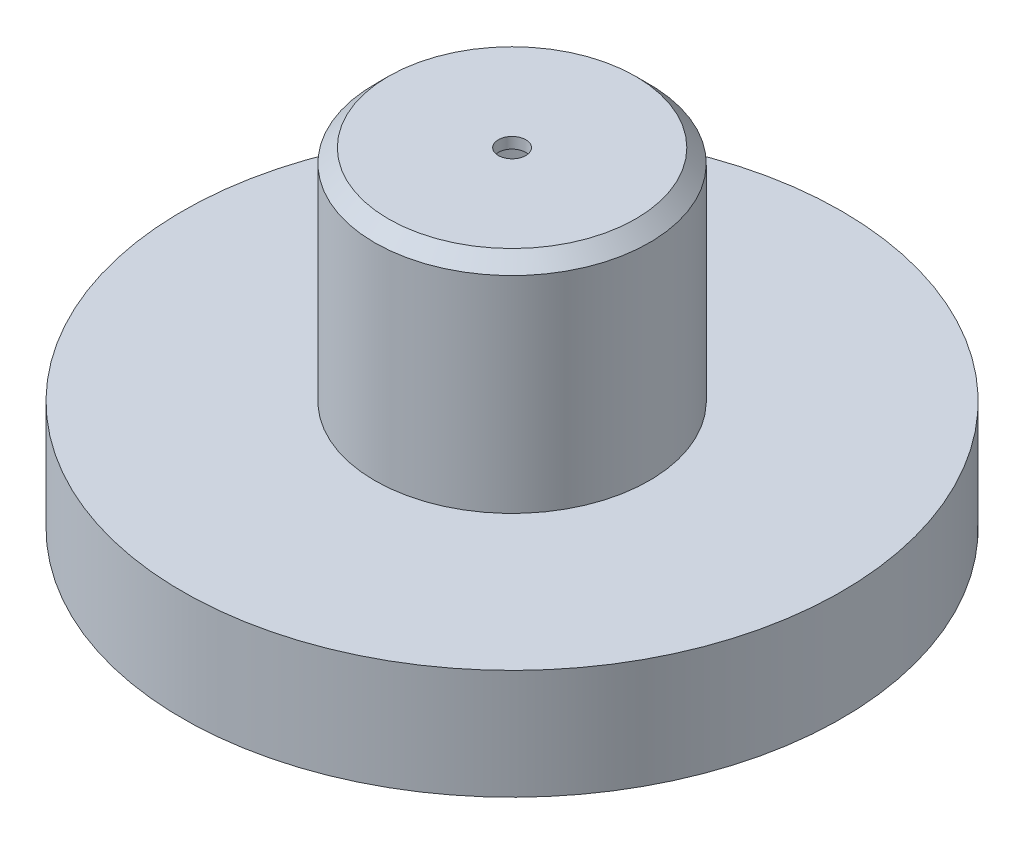
SolidWorks part; units mm, degrees
material "Alloy Steel"
ref_plane "Front Plane" through (0, 0, 0) normal (0, 0, 1) x (1, 0, 0)
ref_plane "Top Plane" through (0, 0, 0) normal (0, 1, 0) x (1, 0, 0)
ref_plane "Right Plane" through (0, 0, 0) normal (1, 0, 0) x (0, 0, -1)
sketch "Sketch2" plane through (0, 0, 0) normal (0, 0, 1) x (1, 0, 0)
  line L0 (55, 0) -> (-55, 0) construction
  line L1 (-75, 50) -> (-70, 50)
  line L2 (-75, 50) -> (-75, 15)
  line L3 (-75, -50) -> (-70, -50)
  line L4 (75, 50) -> (75, 15)
  line L5 (-75, 50) -> (75, -50) construction
  line L6 (-75, -50) -> (75, 50) construction
  line L7 (0, 50) -> (0, -74.3862) construction
  line L8 (-75, -15) -> (-75, -50)
  line L9 (75, -15) -> (75, -50)
  line L10 (-82.5762, 0) -> (133.8676, 0) construction
  line L11 (-60, 50) -> (-35, 50)
  line L12 (-25, 50) -> (25, 50)
  line L13 (35, 50) -> (60, 50)
  line L14 (70, 50) -> (75, 50)
  line L15 (-60, -50) -> (-35, -50)
  line L16 (-25, -50) -> (25, -50)
  line L17 (35, -50) -> (60, -50)
  line L18 (70, -50) -> (75, -50)
  line L19 (-35, 50) -> (-25, 50)
  line L20 (25, 50) -> (35, 50)
  arc A0 (-75, 15) -> (-75, -15) centre (-100.9808, 0) cw
  arc A1 (75, 15) -> (75, -15) centre (100.9808, 0) ccw
  arc A3 (-70, 50) -> (-60, 50) centre (-65, 50) ccw
  arc A4 (-35, -50) -> (-25, -50) centre (-30, -50) cw
  arc A5 (-70, -50) -> (-60, -50) centre (-65, -50) cw
  arc A6 (70, 50) -> (60, 50) centre (65, 50) cw
  arc A8 (70, -50) -> (60, -50) centre (65, -50) ccw
  arc A9 (35, -50) -> (25, -50) centre (30, -50) ccw
  point P0 (0, 0)
  dimension "D3" = 30
  dimension "D8" = 10
  dimension "D1" = 100
  dimension "D2" = 150
  dimension "D4" = 15
  dimension "D5" = 15
  dimension "D7" = 10
extrude "Boss-Extrude1" add sketch "Sketch2" along normal mid plane 200
sketch "Sketch3" plane through (0, 50, 0) normal (0, 1, 0) x (1, 0, 0)
  circle A0 centre (0, 0) radius 55
  circle A1 centre (0, 0) radius 50
  dimension "D1" = 110
  dimension "D2" = 100
extrude "Boss-Extrude3" add sketch "Sketch3" along normal blind 80 contours A1
chamfer "Chamfer1" distance 5 angle 45 1 edges at (0, 130, 50)
fillet "Fillet1" radius 1 4 edges at (75, -50, 0) (-75, -50, 0) (-75, 50, 0) (75, 50, 0)
sketch "Sketch4" plane through (0, -50, 0) normal (0, -1, 0) x (1, 0, 0)
  line L0 (132, 0) -> (-132, 0) construction
  line L1 (0, -132) -> (0, 132) construction
  circle A0 centre (-47.5, 80) radius 5
  circle A1 centre (47.5, 80) radius 5
  circle A2 centre (47.5, 40) radius 5
  circle A3 centre (47.5, 0) radius 5
  circle A4 centre (47.5, -40) radius 5
  circle A5 centre (47.5, -80) radius 5
  circle A6 centre (-47.5, 40) radius 5
  circle A7 centre (-47.5, 0) radius 5
  circle A8 centre (-47.5, -40) radius 5
  circle A9 centre (-47.5, -80) radius 5
  dimension "D3" = 10
  dimension "D1" = 80
  dimension "D2" = 47.5
  dimension "D4" = 2
  dimension "D5" = 5
extrude "Cut-Extrude1" cut sketch "Sketch4" against normal blind 20
sketch "Sketch5" plane through (0, 0, -100) normal (0, 0, -1) x (-1, 0, 0)
  line L0 (132, 0) -> (-132, 0) construction
  line L1 (-55, -15) -> (5, -15)
  line L2 (-55, -15) -> (-55, -25)
  line L3 (-55, -25) -> (5, -25)
  line L4 (5, -15) -> (5, -25)
  line L5 (-55, -15) -> (5, -25) construction
  line L6 (-55, -25) -> (5, -15) construction
  line L7 (-50, 15) -> (0, 15)
  line L8 (-50, 15) -> (-50, 5)
  line L9 (-50, 5) -> (0, 5)
  line L10 (0, 15) -> (0, 5)
  line L11 (-50, 15) -> (0, 5) construction
  line L12 (-50, 5) -> (0, 15) construction
  line L13 (0, 132) -> (0, -132) construction
  circle A0 centre (40, 25) radius 15
  circle A1 centre (35, 25) radius 2.5
  circle A2 centre (45, 25) radius 2.5
  point P0 (-25, -20)
  point P5 (-25, 10)
  dimension "D13" = 30
  dimension "D14" = 5
  dimension "D15" = 5
  dimension "D1" = 25
  dimension "D2" = 40
  dimension "D3" = 5
  dimension "D4" = 5
  dimension "D5" = 10
  dimension "D6" = 25
  dimension "D7" = 20
  dimension "D8" = 25
  dimension "D9" = 10
  dimension "D10" = 50
  dimension "D11" = 60
  dimension "D12" = 10
extrude "Cut-Extrude2" cut sketch "Sketch5" against normal blind 20
sketch "Sketch6" plane through (0, 50, 0) normal (0, 1, 0) x (1, 0, 0)
  line L1 (-75, 100) -> (75, 100)
  line L2 (-75, 100) -> (-75, -100)
  line L3 (-75, -100) -> (75, -100)
  line L4 (75, 100) -> (75, -100)
extrude "Cut-Extrude3" cut sketch "Sketch6" against normal blind 181
sketch "Sketch7" plane through (0, 50, 0) normal (0, -1, 0) x (1, 0, 0)
  circle A0 centre (0, 0) radius 120
extrude "Boss-Extrude4" add sketch "Sketch7" along normal blind 40
sketch "Sketch8" plane through (0, 10, 0) normal (0, -1, 0) x (1, 0, 0)
  circle A0 centre (0, 0) radius 115
sketch "Sketch9" plane through (0, 130, 0) normal (0, 1, 0) x (1, 0, 0)
  circle A0 centre (0, 0) radius 5
shell "Shell1" thickness 4
sketch "Sketch10" plane through (0, 130, 0) normal (0, 1, 0) x (1, 0, 0)
  circle A0 centre (0, 0) radius 5
extrude "Cut-Extrude4" cut sketch "Sketch10" against normal blind 209
